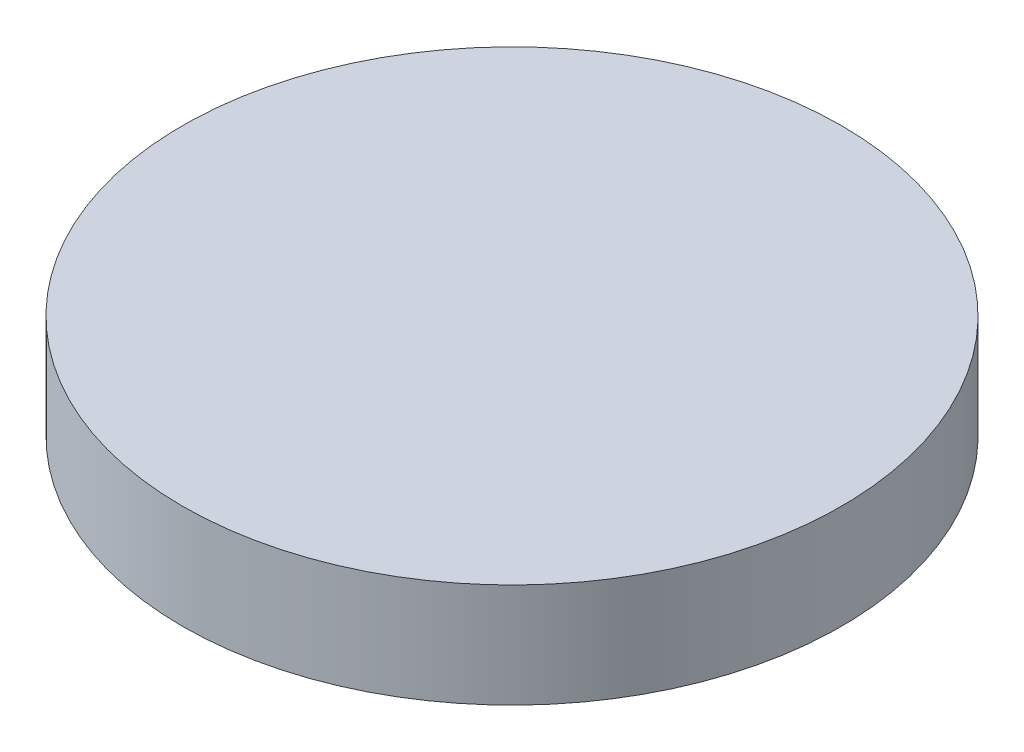
SolidWorks part; units mm, degrees
ref_plane "Front Plane" through (0, 0, 0) normal (0, 0, 1) x (1, 0, 0)
ref_plane "Top Plane" through (0, 0, 0) normal (0, 1, 0) x (1, 0, 0)
ref_plane "Right Plane" through (0, 0, 0) normal (1, 0, 0) x (0, 0, -1)
sketch "Sketch1" plane through (0, 0, 0) normal (0, 1, 0) x (1, 0, 0)
  circle A0 centre (0, 0) radius 60.325
  dimension "D1" = 120.65
extrude "Boss-Extrude1" add sketch "Sketch1" along normal blind 19.05
sketch "Sketch2" plane through (0, 0, 0) normal (0, -1, 0) x (1, 0, 0)
  circle A0 centre (0, 0) radius 57.15
  circle A1 centre (0, 0) radius 55.5625
  dimension "D1" = 114.3
  dimension "D2" = 111.125
extrude "Cut-Extrude1" cut sketch "Sketch2" against normal blind 3.175
sketch "Sketch3" plane through (0, 0, 0) normal (0, -1, 0) x (1, 0, 0)
  line L1 (-4.8486, 3.4631) -> (4.8486, 3.4631)
  line L2 (-4.8486, 3.4631) -> (-4.8486, -3.4631)
  line L3 (-4.8486, -3.4631) -> (4.8486, -3.4631)
  line L4 (4.8486, 3.4631) -> (4.8486, -3.4631)
  line L5 (-4.8486, 3.4631) -> (4.8486, -3.4631) construction
  line L6 (-4.8486, -3.4631) -> (4.8486, 3.4631) construction
  point P0 (0, 0)
extrude "Cut-Extrude2" cut sketch "Sketch3" against normal blind 2.54
